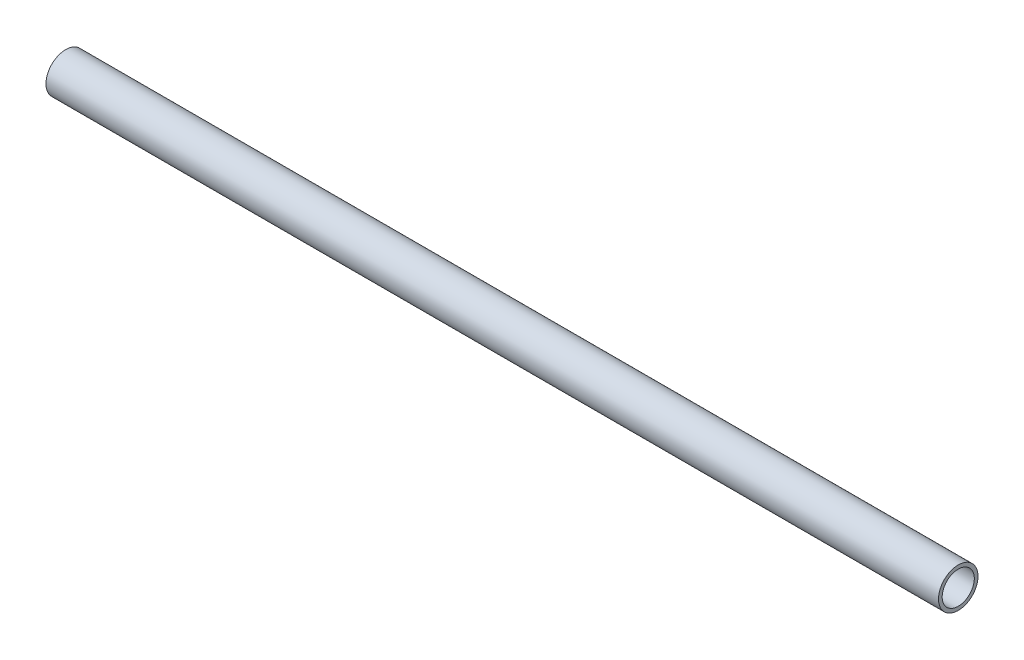
SolidWorks part; units mm, degrees
ref_plane "Front" through (0, 0, 0) normal (0, 0, 1) x (1, 0, 0)
ref_plane "Top" through (0, 0, 0) normal (0, 1, 0) x (1, 0, 0)
ref_plane "Right" through (0, 0, 0) normal (1, 0, 0) x (0, 0, -1)
sketch "Sketch2" plane through (0, 0, 0) normal (0, 0, 1) x (1, 0, 0)
  line L0 (0, 0) -> (358.775, 0)
  dimension "D1" = 358.775
other "Structural Member1"
ref_plane "Plane1" through (0, 0, 0) normal (1, 0, 0) x (0, 1, 0)
sketch "Sketch1" plane through (0, 0, 0) normal (1, 0, 0) x (0, 1, 0)
  circle A0 centre (0, 0) radius 6.4643
  circle A1 centre (0, 0) radius 7.9375
  point P5 (0, 0)
  dimension "Out_dia" = 15.875
  dimension "D1" = 1.4732
